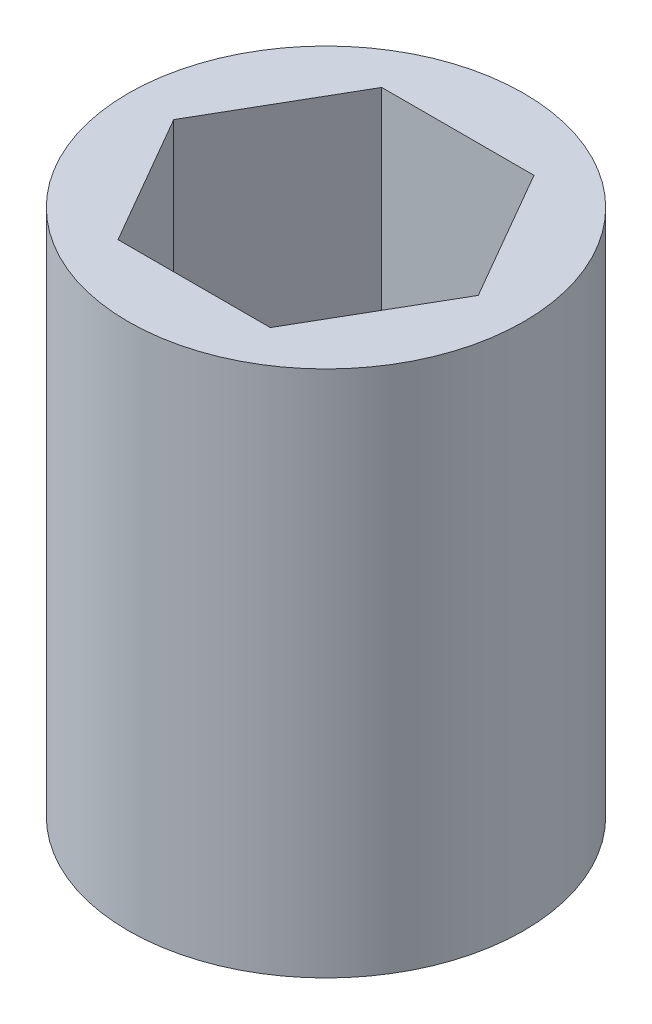
SolidWorks part; units mm, degrees
ref_plane "Front Plane" through (0, 0, 0) normal (0, 0, 1) x (1, 0, 0)
ref_plane "Top Plane" through (0, 0, 0) normal (0, 1, 0) x (1, 0, 0)
ref_plane "Right Plane" through (0, 0, 0) normal (1, 0, 0) x (0, 0, -1)
sketch "Sketch1" plane through (0, 0, 0) normal (0, 1, 0) x (1, 0, 0)
  line L1 (7.3323, 0) -> (3.6662, 6.35)
  line L2 (3.6662, 6.35) -> (-3.6662, 6.35)
  line L3 (-3.6662, 6.35) -> (-7.3323, 0)
  line L4 (-7.3323, 0) -> (-3.6662, -6.35)
  line L5 (-3.6662, -6.35) -> (3.6662, -6.35)
  line L6 (3.6662, -6.35) -> (7.3323, 0)
  circle A0 centre (0, 0) radius 6.35 construction
  circle A1 centre (0, 0) radius 9.525
  dimension "D2" = 19.05
  dimension "D1" = 12.7
extrude "Boss-Extrude1" add sketch "Sketch1" along normal blind 25.4
